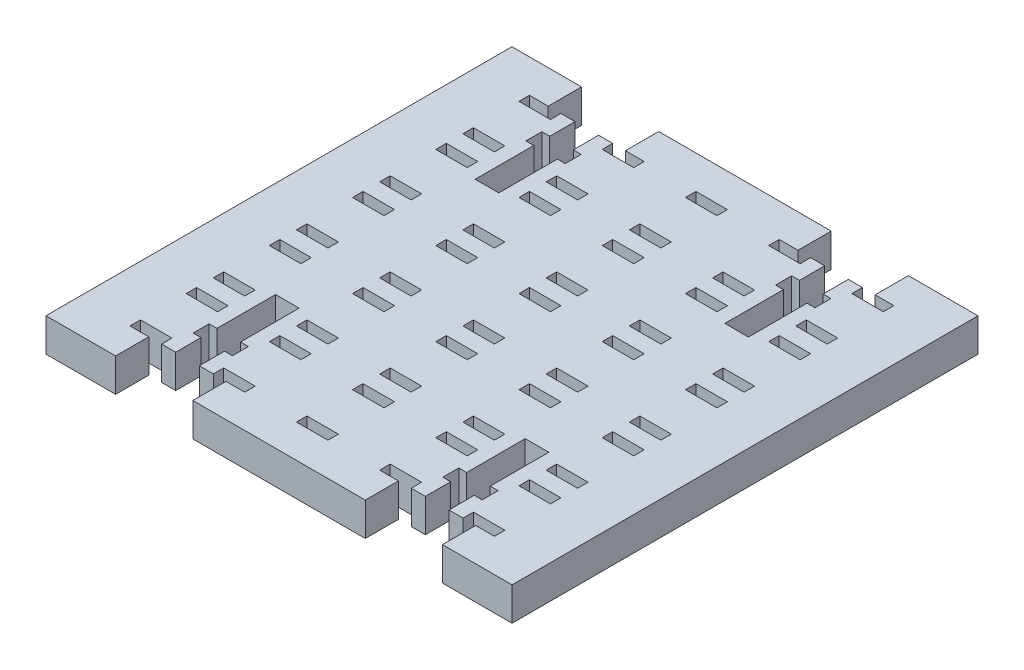
SolidWorks part; units mm, degrees
ref_plane "Front Plane" through (0, 0, 0) normal (0, 0, 1) x (1, 0, 0)
ref_plane "Top Plane" through (0, 0, 0) normal (0, 1, 0) x (1, 0, 0)
ref_plane "Right Plane" through (0, 0, 0) normal (1, 0, 0) x (0, 0, -1)
sketch "Sketch1" plane through (0, 0, 0) normal (0, 1, 0) x (1, 0, 0)
  line L1 (0, 0) -> (168.275, 0)
  line L2 (0, 0) -> (0, -168.275)
  line L3 (0, -168.275) -> (168.275, -168.275)
  line L4 (168.275, 0) -> (168.275, -168.275)
extrude "Boss-Extrude1" add sketch "Sketch1" along normal blind 6.35
sketch "Sketch12" plane through (0, 6.35, 0) normal (0, 1, 0) x (1, 0, 0)
  line L0 (84.1375, 0) -> (84.1375, -6.35) construction
  line L1 (168.275, 0) -> (0, 0) construction
  line L2 (0, -84.1375) -> (6.35, -84.1375) construction
  line L3 (0, 0) -> (0, -168.275) construction
  line L4 (168.275, -84.1375) -> (161.925, -84.1375) construction
  line L5 (168.275, -168.275) -> (168.275, 0) construction
  line L6 (84.1375, -168.275) -> (84.1375, -161.925) construction
  line L7 (0, -168.275) -> (168.275, -168.275) construction
sketch "Sketch13" plane through (0, 6.35, 0) normal (0, 1, 0) x (1, 0, 0)
  line L0 (6.35, -84.1375) -> (6.35, -6.35)
  line L1 (6.35, -6.35) -> (84.1375, -6.35)
  line L2 (84.1375, -6.35) -> (161.925, -6.35)
  line L3 (161.925, -6.35) -> (161.925, -84.1375)
  line L4 (161.925, -84.1375) -> (161.925, -161.925)
  line L5 (161.925, -161.925) -> (84.1375, -161.925)
  line L6 (84.1375, -161.925) -> (6.35, -161.925)
  line L7 (6.35, -161.925) -> (6.35, -84.1375)
sketch "Sketch14" plane through (0, 6.35, 0) normal (0, 1, 0) x (1, 0, 0)
  line L0 (6.35, -84.1375) -> (19.05, -84.1375) construction
  line L1 (19.05, -84.1375) -> (22.225, -84.1375) construction
sketch "Sketch16" plane through (0, 6.35, 0) normal (0, 1, 0) x (1, 0, 0)
  line L0 (19.05, -6.35) -> (19.05, -161.925)
  line L1 (6.35, -6.35) -> (84.1375, -6.35) construction
  line L2 (84.1375, -161.925) -> (6.35, -161.925) construction
  line L3 (22.225, -6.35) -> (22.225, -161.925)
  line L4 (34.925, -6.35) -> (34.925, -161.925)
  line L5 (38.1, -6.35) -> (38.1, -161.925)
  line L6 (50.8, -6.35) -> (50.8, -161.925)
  line L7 (53.975, -6.35) -> (53.975, -161.925)
  line L8 (66.675, -6.35) -> (66.675, -161.925)
  line L9 (69.85, -6.35) -> (69.85, -161.925)
  line L20 (19.05, -6.35) -> (34.925, -6.35) construction
  dimension "D2" = 15.875
  dimension "D1" = 4
sketch "Sketch17" plane through (0, 6.35, 0) normal (0, 1, 0) x (1, 0, 0)
  line L0 (6.35, -6.35) -> (6.35, -19.05) construction
  line L2 (6.35, -84.1375) -> (6.35, -6.35) construction
  line L3 (6.35, -19.05) -> (6.35, -22.225) construction
sketch "Sketch19" plane through (0, 6.35, 0) normal (0, 1, 0) x (1, 0, 0)
  line L0 (6.35, -19.05) -> (161.925, -19.05)
  line L1 (161.925, -6.35) -> (161.925, -84.1375) construction
  line L2 (6.35, -22.225) -> (161.925, -22.225)
  line L3 (6.35, -34.925) -> (161.925, -34.925)
  line L4 (6.35, -38.1) -> (161.925, -38.1)
  line L5 (6.35, -50.8) -> (161.925, -50.8)
  line L6 (6.35, -53.975) -> (161.925, -53.975)
  line L7 (6.35, -66.675) -> (161.925, -66.675)
  line L8 (6.35, -69.85) -> (161.925, -69.85)
  dimension "D1" = 4
sketch "Sketch20" plane through (0, 6.35, 0) normal (0, 1, 0) x (1, 0, 0)
  line L0 (6.35, -6.35) -> (19.05, -19.05) construction
  line L1 (19.05, -6.35) -> (19.05, -161.925) construction
  line L2 (19.05, -6.35) -> (6.35, -19.05) construction
sketch "Sketch21" plane through (0, 6.35, 0) normal (0, 1, 0) x (1, 0, 0)
  line L0 (6.35, -6.35) -> (19.05, -19.05) construction
  circle A0 centre (12.7, -12.7) radius 5
  circle A1 centre (28.575, -12.7) radius 5
  circle A2 centre (44.45, -12.7) radius 5
  circle A3 centre (60.325, -12.7) radius 5
  circle A4 centre (76.2, -12.7) radius 5
  circle A10 centre (28.575, -28.575) radius 5
  circle A11 centre (44.45, -28.575) radius 5
  circle A12 centre (60.325, -28.575) radius 5
  circle A13 centre (76.2, -28.575) radius 5
  circle A19 centre (28.575, -44.45) radius 5
  circle A20 centre (44.45, -44.45) radius 5
  circle A21 centre (60.325, -44.45) radius 5
  circle A22 centre (76.2, -44.45) radius 5
  circle A28 centre (28.575, -60.325) radius 5
  circle A29 centre (44.45, -60.325) radius 5
  circle A30 centre (60.325, -60.325) radius 5
  circle A31 centre (76.2, -60.325) radius 5
  circle A37 centre (28.575, -76.2) radius 5
  circle A38 centre (44.45, -76.2) radius 5
  circle A39 centre (60.325, -76.2) radius 5
  circle A40 centre (76.2, -76.2) radius 5
  circle A91 centre (12.7, -28.575) radius 5
  circle A92 centre (12.7, -44.45) radius 5
  circle A93 centre (12.7, -60.325) radius 5
  circle A94 centre (12.7, -76.2) radius 5
  dimension "D1" = 5
  dimension "D2" = 5
sketch "Sketch22" plane through (0, 6.35, 0) normal (0, 1, 0) x (1, 0, 0)
  line L0 (12.7, -12.7) -> (12.7, -8.35) construction
  line L1 (12.7, -12.7) -> (12.7, -17.05) construction
  line L2 (12.7, -12.7) -> (16.7, -12.7) construction
  line L3 (12.7, -12.7) -> (8.7, -12.7) construction
  line L4 (16.7, -12.7) -> (16.7, -8.35) construction
  line L5 (8.7, -12.7) -> (8.7, -8.35) construction
  line L6 (8.7, -12.7) -> (8.7, -17.05) construction
  line L7 (16.7, -12.7) -> (16.7, -17.05) construction
  line L11 (6.35, -6.35) -> (84.1375, -6.35) construction
  line L17 (12.7, -8.35) -> (15.7, -8.35)
  line L18 (12.7, -8.35) -> (9.7, -8.35)
  line L19 (9.7, -8.35) -> (9.7, -6.35)
  line L20 (15.7, -8.35) -> (15.7, -6.35)
  line L21 (9.7, -6.35) -> (15.7, -6.35)
  line L37 (6.35, -19.05) -> (161.925, -19.05) construction
  line L43 (9.7, -17.05) -> (15.7, -17.05)
  line L44 (15.7, -17.05) -> (15.7, -19.05)
  line L45 (15.7, -19.05) -> (9.7, -19.05)
  line L46 (9.7, -19.05) -> (9.7, -17.05)
extrude "Cut-Extrude1" cut sketch "Sketch22" against normal through all
pattern_linear "LPattern1" count 5 spacing 15.875 along (1, 0, 0) count 5 spacing 15.875 along (0, 0, 1) of "Cut-Extrude1"
sketch "Sketch23" plane through (0, 6.35, 0) normal (0, 1, 0) x (1, 0, 0)
  line L0 (44.45, -44.45) -> (44.45, -6.35) construction
  line L1 (6.35, -6.35) -> (82.55, -6.35)
  line L2 (6.35, -6.35) -> (6.35, -82.55)
  line L3 (6.35, -82.55) -> (82.55, -82.55)
  line L4 (82.55, -6.35) -> (82.55, -82.55)
  line L5 (44.45, -44.45) -> (82.55, -44.45) construction
  line L6 (44.45, -44.45) -> (6.35, -44.45) construction
  line L7 (44.45, -44.45) -> (44.45, -82.55) construction
sketch "Sketch24" plane through (0, 6.35, 0) normal (0, 1, 0) x (1, 0, 0)
  line L0 (76.2, -76.2) -> (82.55, -76.2) construction
  line L1 (76.2, -76.2) -> (76.2, -82.55) construction
  line L2 (12.7, -12.7) -> (12.7, -6.35) construction
  line L3 (12.7, -12.7) -> (6.35, -12.7) construction
  line L4 (6.35, -84.1375) -> (6.35, -6.35) construction
sketch "Sketch26" plane through (0, 6.35, 0) normal (0, 1, 0) x (1, 0, 0)
  line L1 (6.35, -6.35) -> (82.55, -6.35)
  line L2 (6.35, -6.35) -> (6.35, -82.5265)
  line L3 (6.35, -82.5265) -> (82.55, -82.5265)
  line L4 (82.55, -6.35) -> (82.55, -82.5265)
sketch "Sketch27" plane through (0, 6.35, 0) normal (0, 1, 0) x (1, 0, 0)
  line L0 (44.45, -6.35) -> (44.45, 0) construction
  line L1 (6.35, -6.35) -> (82.55, -6.35) construction
  line L2 (82.55, -44.4383) -> (88.9, -44.4383) construction
  line L3 (82.55, -6.35) -> (82.55, -82.5265) construction
  line L4 (6.35, -44.4383) -> (0, -44.4383) construction
  line L5 (6.35, -6.35) -> (6.35, -82.5265) construction
  line L6 (44.45, -82.5265) -> (44.45, -88.8765) construction
  line L7 (6.35, -82.5265) -> (82.55, -82.5265) construction
sketch "Sketch28" plane through (0, 6.35, 0) normal (0, 1, 0) x (1, 0, 0)
  line L1 (0, 0) -> (88.9, 0)
  line L2 (0, 0) -> (0, -88.8765)
  line L3 (0, -88.8765) -> (88.9, -88.8765)
  line L4 (88.9, 0) -> (88.9, -88.8765)
extrude "Cut-Extrude8" cut sketch "Sketch28" against normal through all flip side to cut
sketch "Sketch29" plane through (0, 6.35, 0) normal (0, 1, 0) x (1, 0, 0)
  line L0 (13.275, -6.35) -> (18.3875, -6.35)
  line L1 (0, -44.4383) -> (88.9, -44.4383) construction
  line L2 (0, 0) -> (0, -88.8765) construction
  line L3 (22.8875, -6.35) -> (28, -6.35)
  line L4 (88.9, 0) -> (0, 0) construction
  line L5 (88.9, -88.8765) -> (88.9, 0) construction
  line L6 (18.3875, -6.35) -> (18.3875, -11.176)
  line L7 (22.8875, -74.6525) -> (24.3875, -74.6525)
  line L8 (22.8875, -74.6525) -> (22.8875, -63.4765)
  line L11 (16.8875, -74.6525) -> (18.3875, -74.6525)
  line L12 (22.8875, -77.7005) -> (24.3875, -77.7005)
  line L14 (16.8875, -77.7005) -> (18.3875, -77.7005)
  line L15 (24.3875, -76.1765) -> (24.3875, -74.6525)
  line L17 (16.8875, -76.1765) -> (16.8875, -74.6525)
  line L18 (24.3875, -76.1765) -> (24.3875, -77.7005)
  line L19 (16.8875, -76.1765) -> (16.8875, -77.7005)
  line L20 (13.275, -6.35) -> (13.275, 0)
  line L21 (18.3875, -74.6525) -> (18.3875, -63.4765)
  line L22 (28, -6.35) -> (28, 0)
  line L23 (22.8875, -82.5265) -> (22.8875, -77.7005)
  line L25 (18.3875, -63.4765) -> (22.8875, -63.4765)
  line L27 (13.275, -88.8765) -> (28, -88.8765)
  line L29 (28, -82.5265) -> (28, -88.8765)
  line L31 (13.275, -82.5265) -> (13.275, -88.8765)
  line L33 (18.3875, -82.5265) -> (18.3875, -77.7005)
  line L35 (22.8875, -82.5265) -> (28, -82.5265)
  line L52 (13.275, 0) -> (28, 0)
  line L60 (13.275, -82.5265) -> (18.3875, -82.5265)
  line L69 (44.45, 0) -> (44.45, -88.8765) construction
  line L77 (18.3875, -25.4) -> (22.8875, -25.4)
  line L78 (22.8875, -6.35) -> (22.8875, -11.176)
  line L79 (18.3875, -14.224) -> (18.3875, -25.4)
  line L80 (16.8875, -12.7) -> (16.8875, -11.176)
  line L81 (24.3875, -12.7) -> (24.3875, -11.176)
  line L82 (16.8875, -12.7) -> (16.8875, -14.224)
  line L83 (24.3875, -12.7) -> (24.3875, -14.224)
  line L84 (16.8875, -11.176) -> (18.3875, -11.176)
  line L85 (22.8875, -11.176) -> (24.3875, -11.176)
  line L86 (16.8875, -14.224) -> (18.3875, -14.224)
  line L87 (22.8875, -14.224) -> (22.8875, -25.4)
  line L88 (22.8875, -14.224) -> (24.3875, -14.224)
  line L89 (20.6375, -25.4) -> (20.6375, 0) construction
  line L90 (0, -88.8765) -> (88.9, -88.8765) construction
  line L91 (66.0125, -14.224) -> (64.5125, -14.224)
  line L92 (66.0125, -14.224) -> (66.0125, -25.4)
  line L93 (72.0125, -14.224) -> (70.5125, -14.224)
  line L94 (66.0125, -11.176) -> (64.5125, -11.176)
  line L95 (72.0125, -11.176) -> (70.5125, -11.176)
  line L96 (64.5125, -12.7) -> (64.5125, -14.224)
  line L97 (72.0125, -12.7) -> (72.0125, -14.224)
  line L98 (64.5125, -12.7) -> (64.5125, -11.176)
  line L99 (72.0125, -12.7) -> (72.0125, -11.176)
  line L100 (70.5125, -14.224) -> (70.5125, -25.4)
  line L101 (66.0125, -6.35) -> (66.0125, -11.176)
  line L102 (70.5125, -25.4) -> (66.0125, -25.4)
  line L103 (75.625, -82.5265) -> (70.5125, -82.5265)
  line L104 (75.625, 0) -> (60.9, 0)
  line L105 (66.0125, -82.5265) -> (60.9, -82.5265)
  line L106 (70.5125, -82.5265) -> (70.5125, -77.7005)
  line L107 (75.625, -82.5265) -> (75.625, -88.8765)
  line L108 (60.9, -82.5265) -> (60.9, -88.8765)
  line L109 (75.625, -88.8765) -> (60.9, -88.8765)
  line L110 (70.5125, -63.4765) -> (66.0125, -63.4765)
  line L111 (66.0125, -82.5265) -> (66.0125, -77.7005)
  line L112 (60.9, -6.35) -> (60.9, 0)
  line L113 (70.5125, -74.6525) -> (70.5125, -63.4765)
  line L114 (75.625, -6.35) -> (75.625, 0)
  line L115 (72.0125, -76.1765) -> (72.0125, -77.7005)
  line L116 (64.5125, -76.1765) -> (64.5125, -77.7005)
  line L117 (72.0125, -76.1765) -> (72.0125, -74.6525)
  line L118 (64.5125, -76.1765) -> (64.5125, -74.6525)
  line L119 (72.0125, -77.7005) -> (70.5125, -77.7005)
  line L120 (66.0125, -77.7005) -> (64.5125, -77.7005)
  line L121 (72.0125, -74.6525) -> (70.5125, -74.6525)
  line L122 (66.0125, -74.6525) -> (66.0125, -63.4765)
  line L123 (66.0125, -74.6525) -> (64.5125, -74.6525)
  line L124 (70.5125, -6.35) -> (70.5125, -11.176)
  line L125 (66.0125, -6.35) -> (60.9, -6.35)
  line L126 (75.625, -6.35) -> (70.5125, -6.35)
  line L127 (20.6375, -12.7) -> (24.3875, -12.7) construction
  line L128 (20.6375, -12.7) -> (16.8875, -12.7) construction
  line L129 (15.7, -18.05) -> (18.3875, -18.05) construction
  line L130 (15.7, -19.05) -> (15.7, -17.05) construction
  line L131 (22.8875, -18.05) -> (25.575, -18.05) construction
  line L132 (25.575, -17.05) -> (25.575, -19.05) construction
  line L133 (20.6375, -3.175) -> (13.275, -3.175) construction
  line L134 (20.6375, -3.175) -> (28, -3.175) construction
  line L135 (22.8875, -8.763) -> (20.6375, -8.763) construction
  line L136 (20.6375, -8.763) -> (18.3875, -8.763) construction
  line L137 (20.6375, -18.05) -> (18.3875, -18.05) construction
  line L138 (20.6375, -18.05) -> (22.8875, -18.05) construction
extrude "Cut-Extrude9" cut sketch "Sketch29" against normal through all
